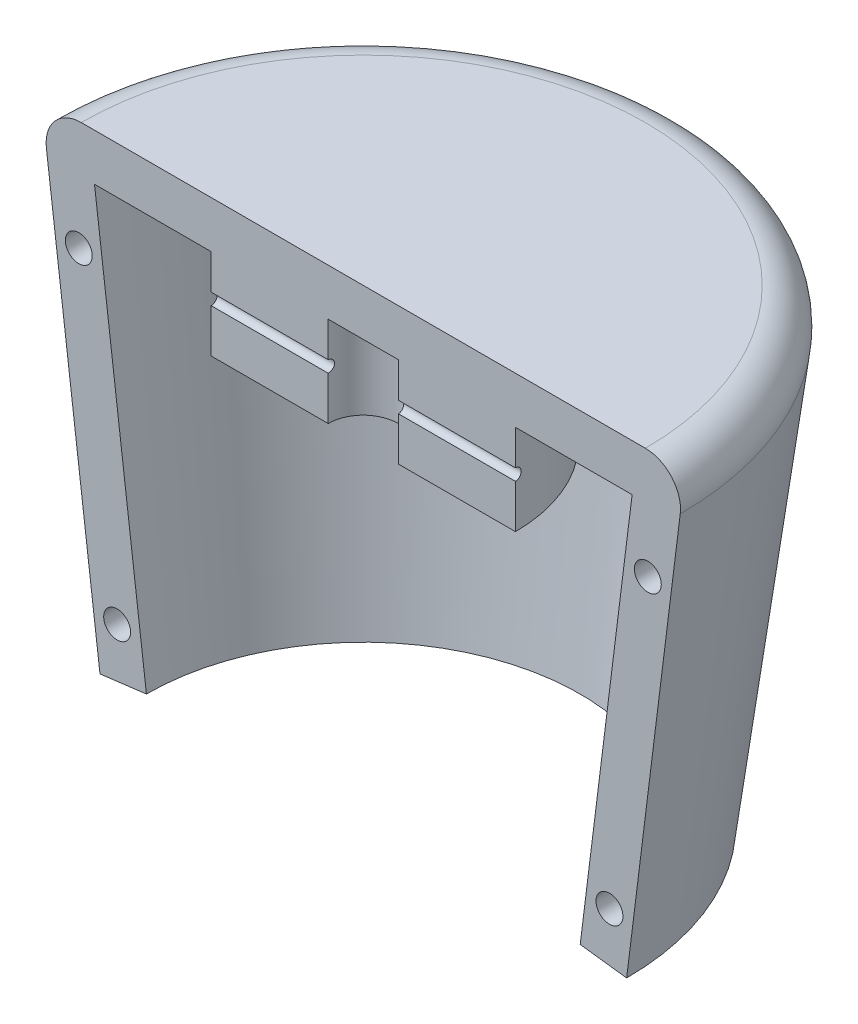
SolidWorks part; units mm, degrees
ref_plane "Front Plane" through (0, 0, 0) normal (0, 0, 1) x (1, 0, 0)
ref_plane "Top Plane" through (0, 0, 0) normal (0, 1, 0) x (1, 0, 0)
ref_plane "Right Plane" through (0, 0, 0) normal (1, 0, 0) x (0, 0, -1)
sketch "Sketch1" plane through (0, 0, 0) normal (0, 0, 1) x (1, 0, 0)
  line L0 (0, 0) -> (0, 40) construction
  line L1 (0, 40) -> (-27.5, 40)
  line L2 (-27.5, 40) -> (-22.5, 0)
  line L3 (0, 36) -> (-3, 36)
  line L4 (-22.9689, 36) -> (-18.5309, 0.4961)
  line L5 (0, 40) -> (0, 36)
  line L6 (-22.5, 0) -> (-18.5309, 0.4961)
  line L7 (-3, 36) -> (-3, 28.277)
  line L8 (-3, 28.277) -> (-13, 28.277)
  line L9 (-13, 28.277) -> (-13, 36)
  line L10 (-13, 36) -> (-22.9689, 36)
  line L11 (0, 36) -> (-22.9689, 36) construction
  dimension "D1" = 27.5
  dimension "D2" = 40
  dimension "D3" = 22.5
  dimension "D5" = 3
  dimension "D6" = 10
  dimension "D4" = 4
revolve "Revolve1" add sketch "Sketch1" angle 180 about L5
fillet "Fillet1" radius 3 1 edges at (0, 40, -27.5)
sketch "Sketch2" plane through (0, 0, 0) normal (0, 0, 1) x (1, 0, 0)
  line L1 (-14, 32.5) -> (16, 32.5)
  line L2 (-14, 32.5) -> (-14, 33)
  line L3 (-14, 33) -> (16, 33)
  line L4 (16, 32.5) -> (16, 33)
  line L5 (-3, 36) -> (3, 36) construction
  line L6 (-13, 36) -> (-13, 28.277) construction
  dimension "D1" = 0.5
  dimension "D2" = 3
  dimension "D3" = 30
  dimension "D4" = 1
revolve "Cut-Revolve1" cut sketch "Sketch2" angle 360 about L1
sketch "Sketch3" plane through (0, 0, 0) normal (0, 0, 1) x (1, 0, 0)
  line L0 (-27.0785, 36.6279) -> (-22.5, 0) construction
  line L1 (27.0785, 36.6279) -> (22.5, 0) construction
  circle A0 centre (-24.3097, 30.6025) radius 1.15
  circle A1 centre (-21.0338, 4.3952) radius 1.15
  circle A2 centre (21.0338, 4.3952) radius 1.15
  circle A3 centre (24.3097, 30.6025) radius 1.15
  point P8 (0, 0)
  point P11 (0, 0)
  point P14 (0, 0)
  point P15 (0, 0)
  dimension "D2" = 2.3
  dimension "D1" = 2
  dimension "D3" = 2
  dimension "D4" = 2
  dimension "D5" = 2
extrude "Cut-Extrude1" cut sketch "Sketch3" against normal blind 5
